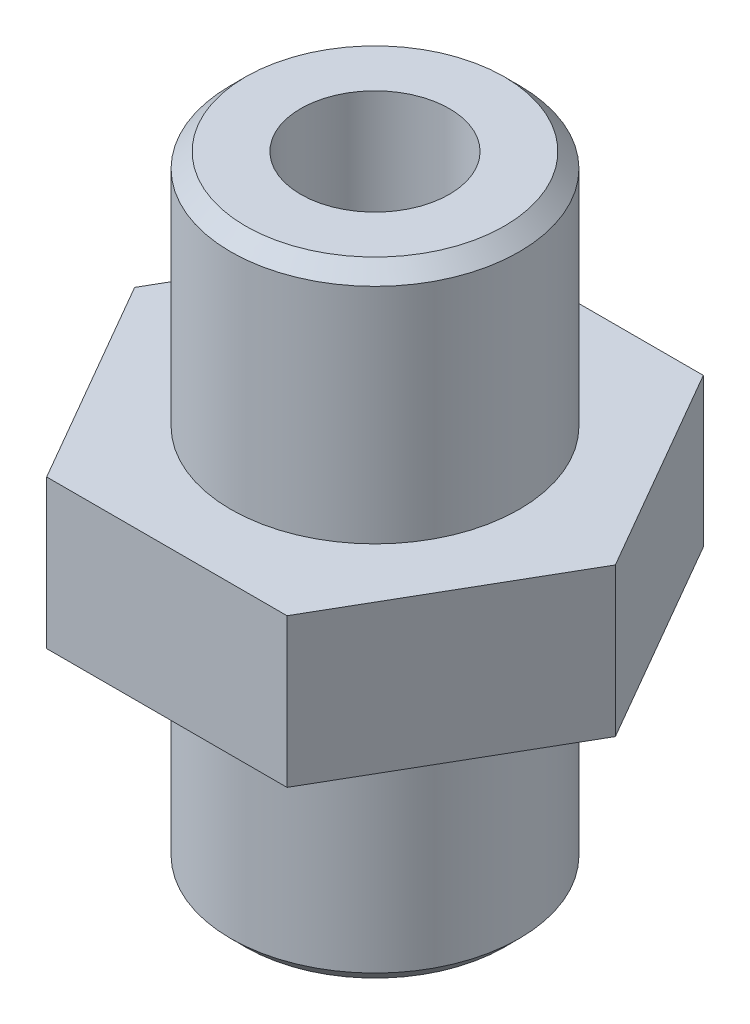
SolidWorks part; units mm, degrees
material "1.6523 (20NiCrMoS2-2)"
ref_plane "Front Plane" through (0, 0, 0) normal (0, 0, 1) x (1, 0, 0)
ref_plane "Top Plane" through (0, 0, 0) normal (0, 1, 0) x (1, 0, 0)
ref_plane "Right Plane" through (0, 0, 0) normal (1, 0, 0) x (0, 0, -1)
sketch "Sketch1" plane through (0, 0, 0) normal (0, 1, 0) x (1, 0, 0)
  line L1 (4.0415, -7) -> (8.0829, 0)
  line L2 (8.0829, 0) -> (4.0415, 7)
  line L3 (4.0415, 7) -> (-4.0415, 7)
  line L4 (-4.0415, 7) -> (-8.0829, 0)
  line L5 (-8.0829, 0) -> (-4.0415, -7)
  line L6 (-4.0415, -7) -> (4.0415, -7)
  circle A0 centre (0, 0) radius 7 construction
  dimension "D1" = 14
extrude "Boss-Extrude1" add sketch "Sketch1" along normal blind 5
sketch "Sketch2" plane through (0, 5, 0) normal (0, 1, 0) x (1, 0, 0)
  circle A0 centre (0, 0) radius 4.85
  dimension "D1" = 9.7
extrude "Boss-Extrude2" add sketch "Sketch2" along normal blind 8
sketch "Sketch3" plane through (0, 0, 0) normal (0, -1, 0) x (1, 0, 0)
  circle A0 centre (0, 0) radius 4.85
  dimension "D1" = 9.7
extrude "Boss-Extrude3" add sketch "Sketch3" along normal blind 8
chamfer "Chamfer1" distance 0.5 angle 45 2 edges at (0, -8, -4.85) (0, 13, 4.85)
sketch "Sketch4" plane through (0, 13, 0) normal (0, 1, 0) x (1, 0, 0)
  circle A0 centre (0, 0) radius 2.5
  dimension "D1" = 5
extrude "Cut-Extrude1" cut sketch "Sketch4" against normal through all
